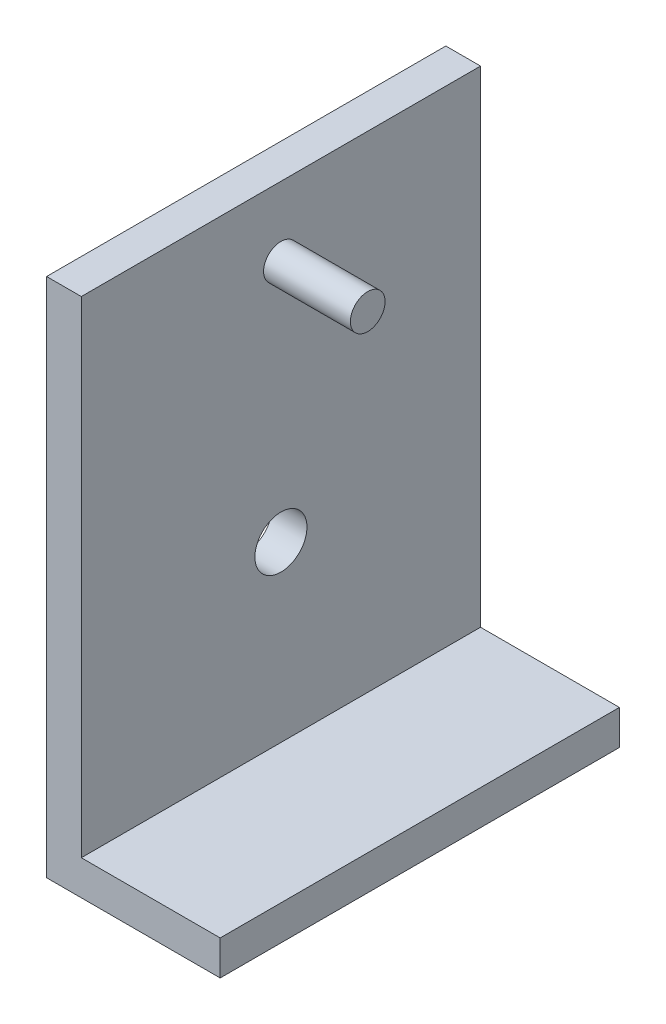
SolidWorks part; units mm, degrees
ref_plane "Front Plane" through (0, 0, 0) normal (0, 0, 1) x (1, 0, 0)
ref_plane "Top Plane" through (0, 0, 0) normal (0, 1, 0) x (1, 0, 0)
ref_plane "Right Plane" through (0, 0, 0) normal (1, 0, 0) x (0, 0, -1)
sketch "Sketch1" plane through (0, 0, 0) normal (0, 0, 1) x (1, 0, 0)
  line L0 (0, 150) -> (0, 0)
  line L1 (0, 0) -> (50, 0)
  line L2 (50, 0) -> (50, 10)
  line L3 (50, 10) -> (10, 10)
  line L4 (10, 10) -> (10, 150)
  line L5 (10, 150) -> (0, 150)
  line L6 (55, 0) -> (-55, 0) construction
  line L7 (0, -55) -> (0, 55) construction
  dimension "D1" = 10
  dimension "D2" = 10
  dimension "D3" = 150
  dimension "D4" = 50
extrude "Boss-Extrude1" add sketch "Sketch1" along normal mid plane 115
sketch "Sketch2" plane through (0, 0, 0) normal (-1, 0, 0) x (0, 0, 1)
  circle A0 centre (0, 60) radius 7.5
extrude "Cut-Extrude1" cut sketch "Sketch2" against normal through all
sketch "Sketch3" plane through (10, 0, 0) normal (1, 0, 0) x (0, 0, -1)
  line L0 (-57.5, 150) -> (57.5, 150) construction
  circle A0 centre (0, 130) radius 5
  dimension "D1" = 10
  dimension "D2" = 20
extrude "Boss-Extrude2" add sketch "Sketch3" along normal blind 25
